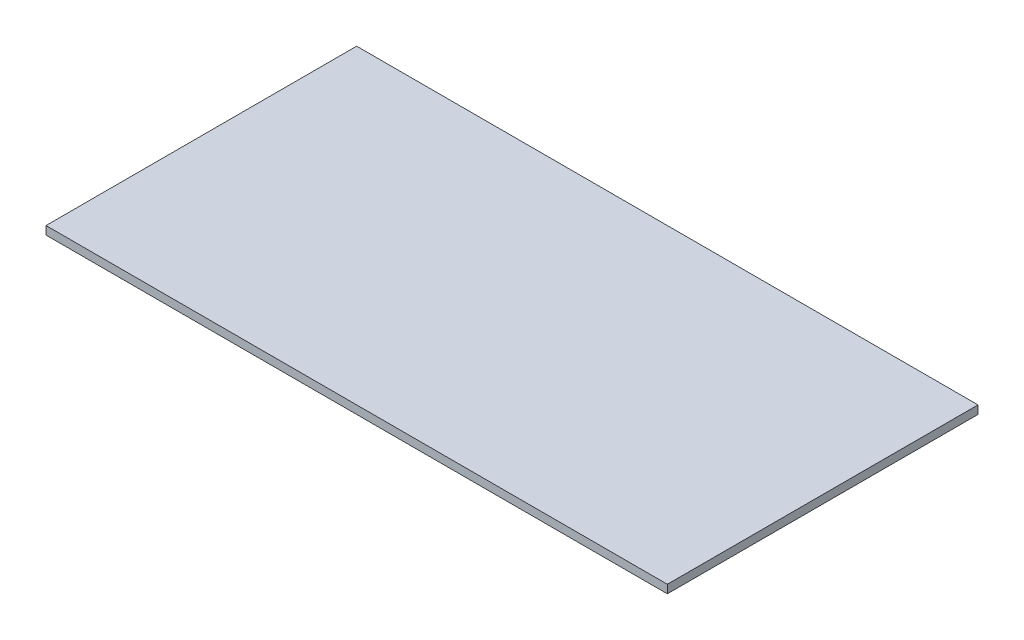
SolidWorks part; units mm, degrees
ref_plane "Front Plane" through (0, 0, 0) normal (0, 0, 1) x (1, 0, 0)
ref_plane "Top Plane" through (0, 0, 0) normal (0, 1, 0) x (1, 0, 0)
ref_plane "Right Plane" through (0, 0, 0) normal (1, 0, 0) x (0, 0, -1)
sketch "Sketch1" plane through (0, 0, 0) normal (0, 1, 0) x (1, 0, 0)
  line L1 (-750, -375) -> (750, -375)
  line L2 (-750, -375) -> (-750, 375)
  line L3 (-750, 375) -> (750, 375)
  line L4 (750, -375) -> (750, 375)
  line L5 (-750, -375) -> (750, 375) construction
  line L6 (-750, 375) -> (750, -375) construction
  point P0 (0, 0)
  dimension "D1" = 1500
  dimension "D2" = 750
extrude "Boss-Extrude1" add sketch "Sketch1" along normal blind 20
